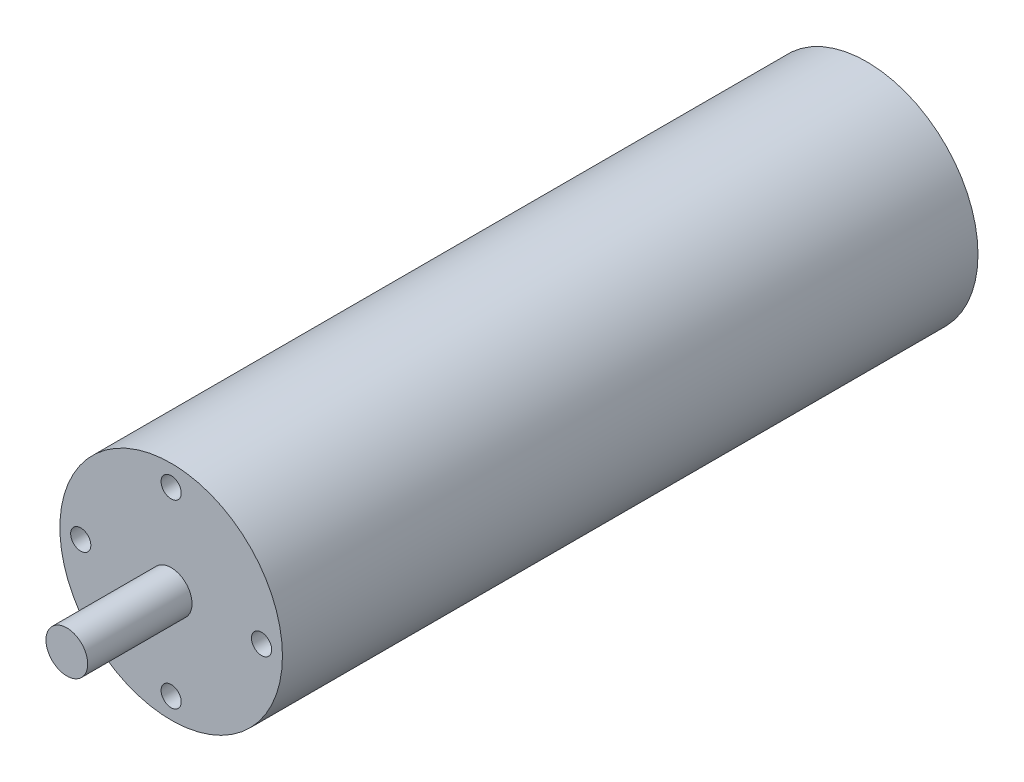
SolidWorks part; units mm, degrees
ref_plane "Front Plane" through (0, 0, 0) normal (0, 0, 1) x (1, 0, 0)
ref_plane "Top Plane" through (0, 0, 0) normal (0, 1, 0) x (1, 0, 0)
ref_plane "Right Plane" through (0, 0, 0) normal (1, 0, 0) x (0, 0, -1)
sketch "Sketch1" plane through (0, 0, 0) normal (0, 0, 1) x (1, 0, 0)
  circle A0 centre (0, 0) radius 16
  dimension "D1" = 32
extrude "Boss-Extrude1" add sketch "Sketch1" along normal blind 100
sketch "Sketch2" plane through (0, 0, 100) normal (0, 0, 1) x (1, 0, 0)
  circle A0 centre (0, 0) radius 3
  dimension "D1" = 6
extrude "Boss-Extrude2" add sketch "Sketch2" along normal blind 15
sketch "Sketch4" plane through (0, 0, 100) normal (0, 0, 1) x (1, 0, 0)
  circle A0 centre (0, 0) radius 13 construction
  point P3 (0, 13)
  dimension "D1" = 26
hole_wizard "M3.5x0.6 Tapped Hole1" positions "Sketch5" profile "Sketch6" tap size "M3.5x0.6" standard "ANSI Metric"
sketch "Sketch5" plane through (0, 0, 100) normal (0, 0, 1) x (1, 0, 0)
  point P0 (0, 13)
sketch "Sketch6" plane through (0, 13, 100) normal (1, 0, 0) x (0, -1, 0)
  line L0 (0, 0) -> (0, 9.7612)
  line L1 (0, 9.7612) -> (1.45, 8.89)
  line L2 (1.45, 8.89) -> (1.45, 0)
  line L5 (1.45, 0) -> (0, 0)
  line L10 (0, 9.7612) -> (-1.45, 8.89) construction
  line L11 (0, -6.35) -> (0, 107.95) construction
  dimension "Tap Drill Dia." = 2.9
  dimension "Tap Drill Depth" = 8.89
  dimension "Drill Angle" = 118
cosmetic thread "Hole Thread1" parameters "D1"=7.112, "D2"=3.5
pattern_circular "CirPattern1" count 4 over 360 about axis through (0, 0, 0) along (0, 0, 1) of "M3.5x0.6 Tapped Hole1"
